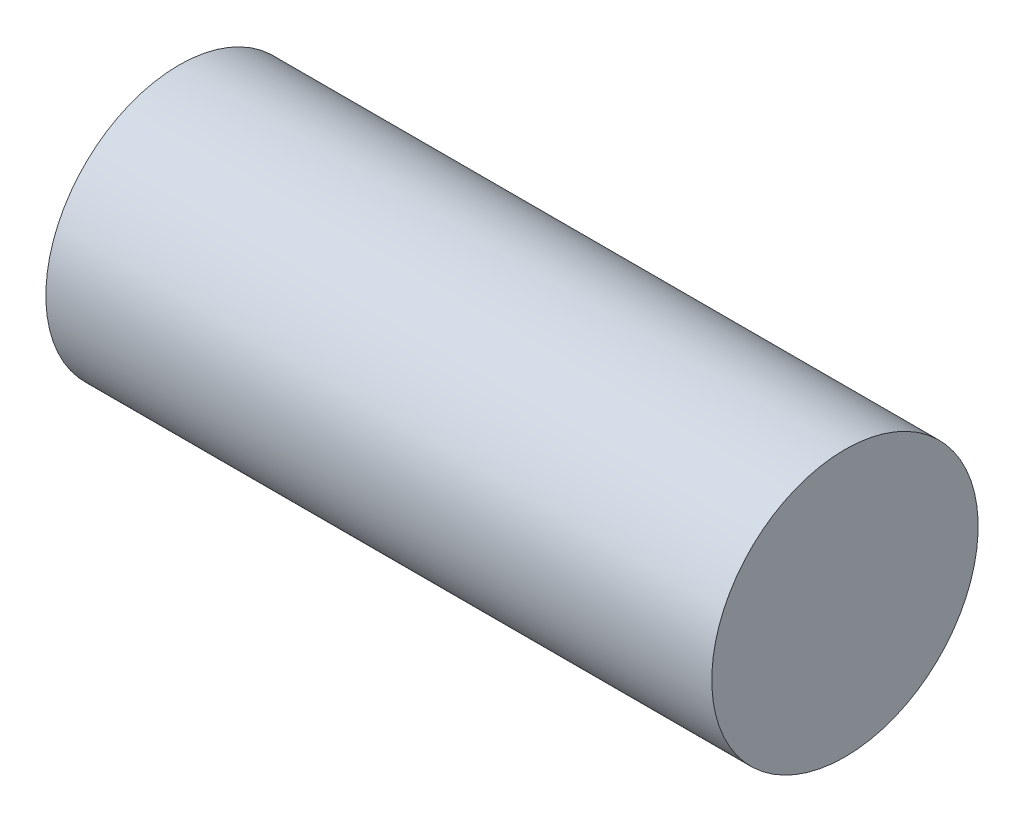
SolidWorks part; units mm, degrees
ref_plane "Front Plane" through (0, 0, 0) normal (0, 0, 1) x (1, 0, 0)
ref_plane "Top Plane" through (0, 0, 0) normal (0, 1, 0) x (1, 0, 0)
ref_plane "Right Plane" through (0, 0, 0) normal (1, 0, 0) x (0, 0, -1)
sketch "Sketch2" plane through (0, 0, 0) normal (0, 0, 1) x (1, 0, 0)
  line L0 (5, 0) -> (5, 50)
  line L1 (-5, 0) -> (-5, 50)
  line L2 (-75, -5) -> (75, -5)
  arc A0 (-5, 0) -> (5, 0) centre (0, 0) ccw
  point P9 (0, -5)
sweep "Sweep1" add path "Sketch2" circular profile diameter 60 parameters "D3"=60
